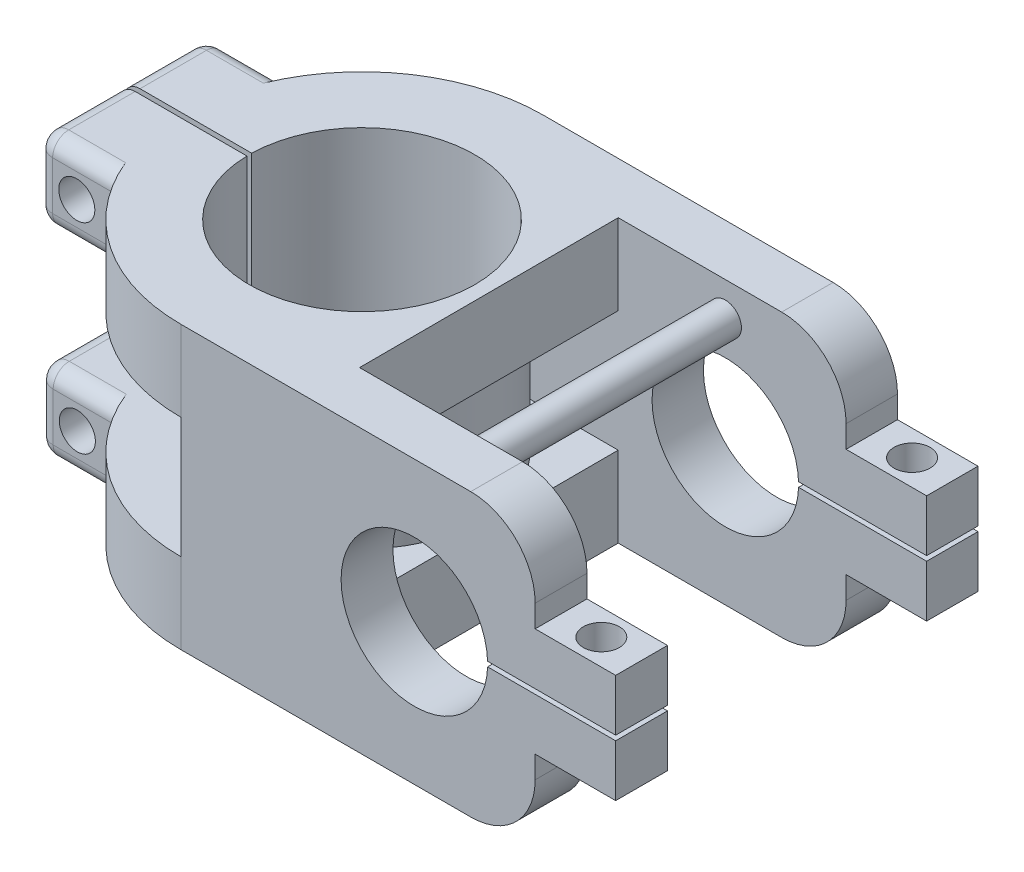
SolidWorks part; units mm, degrees
ref_plane "Front Plane" through (0, 0, 0) normal (0, 0, 1) x (1, 0, 0)
ref_plane "Top Plane" through (0, 0, 0) normal (0, 1, 0) x (1, 0, 0)
ref_plane "Right Plane" through (0, 0, 0) normal (1, 0, 0) x (0, 0, -1)
sketch "Sketch2" plane through (0, 0, 0) normal (0, 1, 0) x (1, 0, 0)
  circle A0 centre (0, 0) radius 17.78
  circle A2 centre (0, 0) radius 28.575
  dimension "D1" = 35.56
  dimension "D2" = 57.15
extrude "Boss-Extrude3" add sketch "Sketch2" along normal blind 12.7
sketch "Sketch3" plane through (0, 12.7, 0) normal (0, 1, 0) x (1, 0, 0)
  line L0 (0, 0) -> (20.2056, -20.2056) construction
  line L1 (0, 0) -> (20.2056, 20.2056) construction
  line L2 (0, 0) -> (-28.575, 0) construction
  line L3 (-25.3321, 0) -> (-25.3321, 13.2218) construction
  line L4 (-25.3321, 13.2218) -> (-25.3321, -13.2218)
  line L5 (-25.3321, 13.2218) -> (-36.1866, 13.2218)
  line L6 (-36.1866, 13.2218) -> (-36.1866, -13.2218)
  line L7 (-36.1866, -13.2218) -> (-25.3321, -13.2218)
  circle A0 centre (0, 0) radius 28.575 construction
extrude "Cut-Extrude1" cut sketch "Sketch3" against normal blind 12.7
sketch "Sketch4" plane through (0, 12.7, 0) normal (0, 1, 0) x (1, 0, 0)
  line L0 (0, 0) -> (-25.3321, 0) construction
  line L1 (-25.3321, -13.2218) -> (-25.3321, 13.2218) construction
  line L2 (-16.3768, 0) -> (-16.3768, 0.381)
  line L3 (-16.3768, 0) -> (-16.3768, -0.381)
  line L4 (-16.3768, 0.381) -> (-26.0036, 0.381)
  line L5 (-16.3768, -0.381) -> (-26.0036, -0.381)
  line L6 (-26.0036, -0.381) -> (-26.0036, 0.381)
  dimension "D1" = 0.762
extrude "Cut-Extrude2" cut sketch "Sketch4" against normal blind 12.7
sketch "Sketch5" plane through (-25.3321, 0, 0) normal (-1, 0, 0) x (0, 0, 1)
  line L1 (0.381, 12.7) -> (13.2218, 12.7)
  line L2 (0.381, 12.7) -> (0.381, 0)
  line L3 (0.381, 0) -> (13.2218, 0)
  line L4 (13.2218, 12.7) -> (13.2218, 0)
extrude "Boss-Extrude4" add sketch "Sketch5" along normal blind 12.7
sketch "Sketch6" plane through (-25.3321, 0, 0) normal (-1, 0, 0) x (0, 0, 1)
  line L1 (-13.2218, 12.7) -> (-0.381, 12.7)
  line L2 (-13.2218, 12.7) -> (-13.2218, 0)
  line L3 (-13.2218, 0) -> (-0.381, 0)
  line L4 (-0.381, 12.7) -> (-0.381, 0)
extrude "Boss-Extrude5" add sketch "Sketch6" along normal blind 12.7
sketch "Sketch7" plane through (0, 0, 13.2218) normal (0, 0, 1) x (1, 0, 0)
  line L0 (-31.6821, 12.7) -> (-31.6821, 0) construction
  line L1 (-38.0321, 12.7) -> (-25.3321, 12.7) construction
  line L2 (-38.0321, 0) -> (-25.3321, 0) construction
  circle A0 centre (-31.6821, 6.35) radius 2.8448
extrude "Cut-Extrude3" cut sketch "Sketch7" against normal blind 33.02
fillet "Fillet1" radius 2.54 1 edges at (-38.0321, 6.35, 13.2218)
fillet "Fillet2" radius 2.54 1 edges at (-38.0321, 6.35, -13.2218)
fillet "Fillet3" radius 2.54 3 edges at (-30.4121, 12.7, -13.2218) (-37.2882, 12.7, -12.4778) (-38.0321, 12.7, -5.5314)
fillet "Fillet4" radius 2.54 3 edges at (-30.4121, 12.7, 13.2218) (-37.2882, 12.7, 12.4778) (-38.0321, 12.7, 5.5314)
fillet "Fillet5" radius 2.54 3 edges at (-30.4121, 0, -13.2218) (-37.2882, 0, -12.4778) (-38.0321, 0, -5.5314)
fillet "Fillet6" radius 2.54 3 edges at (-30.4121, 0, 13.2218) (-37.2882, 0, 12.4778) (-38.0321, 0, 5.5314)
sketch "Sketch8" plane through (0, 12.7, 0) normal (0, 1, 0) x (1, 0, 0)
  circle A0 centre (0, 0) radius 18.7388
  circle A1 centre (0, 0) radius 17.78
extrude "Boss-Extrude6" add sketch "Sketch8" along normal blind 19.05
sketch "Sketch9" plane through (0, 31.75, 0) normal (0, 1, 0) x (1, 0, 0)
  circle A0 centre (0, 0) radius 28.575
extrude "Boss-Extrude7" add sketch "Sketch9" along normal blind 12.7
sketch "Sketch12" plane through (0, 44.45, 0) normal (0, 1, 0) x (1, 0, 0)
  line L0 (0, 0) -> (-28.575, 0) construction
  line L1 (-25.2365, 13.4034) -> (-25.2365, -13.4034)
  line L2 (-25.2365, 13.4034) -> (-36.6122, 13.4034)
  line L3 (-25.2365, -13.4034) -> (-36.6122, -13.4034)
  line L4 (-36.6122, -13.4034) -> (-36.6122, 13.4034)
  circle A0 centre (0, 0) radius 28.575 construction
extrude "Cut-Extrude4" cut sketch "Sketch12" against normal blind 12.7
sketch "Sketch13" plane through (-25.2365, 0, 0) normal (-1, 0, 0) x (0, 0, 1)
  line L0 (-18.7388, 31.75) -> (18.7388, 31.75) construction
  line L1 (-13.4034, 44.45) -> (13.4034, 44.45)
  line L2 (-13.4034, 44.45) -> (-13.4034, 31.75)
  line L3 (-13.4034, 31.75) -> (13.4034, 31.75)
  line L4 (13.4034, 44.45) -> (13.4034, 31.75)
  line L5 (13.4034, 31.75) -> (-13.4034, 31.75) construction
extrude "Boss-Extrude8" add sketch "Sketch13" along normal blind 12.7
sketch "Sketch14" plane through (0, 44.45, 0) normal (0, 1, 0) x (1, 0, 0)
  circle A0 centre (0, 0) radius 17.78
extrude "Cut-Extrude5" cut sketch "Sketch14" against normal blind 12.7
sketch "Sketch15" plane through (0, 44.45, 0) normal (0, 1, 0) x (1, 0, 0)
  line L0 (-37.9365, 0) -> (0, 0)
  line L1 (-37.9365, -13.4034) -> (-37.9365, 13.4034) construction
  line L2 (0, 0) -> (0, 0.381)
  line L3 (0, 0.381) -> (-38.0321, 0.381)
  line L4 (-38.0321, 0.381) -> (-37.9365, 0)
  line L5 (0, 0) -> (0, -0.381)
  line L6 (0, -0.381) -> (-37.9365, -0.381)
  line L7 (-37.9365, -0.381) -> (-37.9365, 0)
  line L8 (-37.9365, 0) -> (0, 0)
  circle M6 centre (0, 0) radius 17.78
  line M9 (-37.9365, 13.4034) -> (-37.9365, -13.4034)
  dimension "D1" = 0.381
extrude "Cut-Extrude6" cut sketch "Sketch15" against normal blind 12.7 contours L3 L0 M6 M9
sketch "Sketch16" plane through (0, 44.45, 0) normal (0, 1, 0) x (1, 0, 0)
  line L6 (-37.9365, 0) -> (-16.9968, 0)
  line L7 (-37.9365, 0) -> (-37.9365, -0.381)
  line L8 (-37.9365, -0.381) -> (-16.9968, -0.381)
  line L9 (-16.9968, 0) -> (-16.9968, -0.381)
  dimension "D1" = 0.381
extrude "Cut-Extrude7" cut sketch "Sketch16" against normal blind 12.7
fillet "Fillet7" radius 2.54 1 edges at (-37.9365, 44.45, -6.8922)
fillet "Fillet8" radius 2.54 1 edges at (-37.9365, 44.45, 6.8922)
fillet "Fillet9" radius 2.54 1 edges at (-37.9365, 31.75, -6.8922)
fillet "Fillet10" radius 2.54 1 edges at (-37.9365, 31.75, 6.8922)
fillet "Fillet11" radius 2.54 5 edges at (-30.3165, 31.75, 13.4034) (-37.1925, 32.4939, 13.4034) (-30.3165, 44.45, 13.4034) (-37.1925, 43.7061, 13.4034) (-37.9365, 38.1, 13.4034)
fillet "Fillet12" radius 2.54 5 edges at (-30.3165, 44.45, -13.4034) (-37.1925, 43.7061, -13.4034) (-30.3165, 31.75, -13.4034) (-37.1925, 32.4939, -13.4034) (-37.9365, 38.1, -13.4034)
sketch "Sketch17" plane through (0, 0, 13.4034) normal (0, 0, 1) x (1, 0, 0)
  line L0 (-25.2365, 38.1) -> (-37.9365, 38.1) construction
  line L1 (-25.2365, 34.29) -> (-25.2365, 41.91) construction
  line L2 (-37.9365, 34.29) -> (-37.9365, 41.91) construction
  circle A0 centre (-31.5865, 38.1) radius 2.8448
extrude "Cut-Extrude8" cut sketch "Sketch17" against normal blind 29.464
sketch "Sketch19" plane through (0, 31.75, 0) normal (0, 1, 0) x (1, 0, 0)
  line L5 (-18.7349, 0.381) -> (-16.9078, 0.381)
  line L6 (-18.7349, 0.381) -> (-18.7349, -0.381)
  line L7 (-18.7349, -0.381) -> (-16.9078, -0.381)
  line L8 (-16.9078, 0.381) -> (-16.9078, -0.381)
extrude "Cut-Extrude13" cut sketch "Sketch19" against normal blind 29.464
sketch "Sketch22" plane through (0, 12.7, 0) normal (0, 1, 0) x (1, 0, 0)
  line L0 (0, 0) -> (0, -18.7388) construction
  line L1 (0, -18.7388) -> (0, -20.3979) construction
  line L2 (0, -20.3979) -> (0, -28.575)
  line L3 (0, -28.575) -> (55.88, -28.575)
  line L4 (55.88, -28.575) -> (55.88, -20.3979)
  line L5 (55.88, -20.3979) -> (0, -20.3979)
  arc A0 (-18.7349, -0.381) -> (-18.7349, 0.381) centre (0, 0) ccw construction
  arc A1 (-26.5034, -10.6818) -> (-26.5034, 10.6818) centre (0, 0) ccw construction
  dimension "D1" = 55.88
extrude "Boss-Extrude12" add sketch "Sketch22" along normal blind 31.75 and the other way blind 12.7
sketch "Sketch23" plane through (0, 12.7, 0) normal (0, 1, 0) x (1, 0, 0)
  line L0 (0, -20.3979) -> (0, -18.6659) construction
  line L1 (0, 18.7388) -> (0, 20.4709) construction
  line L2 (0, 20.4709) -> (0, 28.575)
  line L3 (0, 28.575) -> (55.88, 28.575)
  line L4 (0, 20.4709) -> (55.88, 20.4709)
  line L5 (55.88, 20.4709) -> (55.88, 28.575)
  arc A0 (-18.7349, -0.381) -> (-18.7349, 0.381) centre (0, 0) ccw construction
  arc A1 (20.0114, -20.3979) -> (-26.5034, 10.6818) centre (0, 0) ccw construction
  dimension "D1" = 1.7321
  dimension "D2" = 55.88
extrude "Boss-Extrude13" add sketch "Sketch23" along normal blind 31.75 and the other way blind 12.7
sketch "Sketch24" plane through (0, 0, -28.575) normal (0, 0, -1) x (-1, 0, 0)
  line L0 (-17.78, 22.225) -> (-55.88, 22.225) construction
  line L2 (-17.78, 44.45) -> (-17.78, 0) construction
  line L3 (-55.88, 44.45) -> (0, 44.45) construction
  line L4 (-55.88, 0) -> (-55.88, 44.45) construction
  circle A0 centre (-36.83, 22.225) radius 11.557
extrude "Cut-Extrude14" cut sketch "Sketch24" against normal blind 67.31
fillet "Fillet13" radius 10.16 1 edges at (55.88, 44.45, 24.4865)
fillet "Fillet14" radius 10.16 1 edges at (55.88, 0, 24.4865)
fillet "Fillet15" radius 10.16 1 edges at (55.88, 44.45, -24.5229)
fillet "Fillet16" radius 10.16 1 edges at (55.88, 0, -24.5229)
sketch "Sketch25" plane through (0, 44.45, 0) normal (0, 1, 0) x (1, 0, 0)
  line L0 (28.575, 0.0522) -> (28.575, 20.4709)
  line L1 (19.9368, 20.4709) -> (45.72, 20.4709) construction
  line L2 (28.575, 20.4709) -> (19.9368, 20.4709)
  line L3 (19.9368, 20.4709) -> (20.0114, -20.3979)
  line L4 (20.0114, -20.3979) -> (28.575, -20.3979)
  line L5 (45.72, -20.3979) -> (20.0114, -20.3979) construction
  line L6 (28.575, -20.3979) -> (28.575, 0.0522)
  arc A0 (20.0114, -20.3979) -> (19.9368, 20.4709) centre (0, 0) ccw construction
extrude "Cut-Extrude15" cut sketch "Sketch25" against normal blind 67.31
sketch "Sketch26" plane through (0, 0, -20.4709) normal (0, 0, 1) x (1, 0, 0)
  line L0 (36.83, 33.782) -> (36.83, 44.45) construction
  line L1 (19.9368, 44.45) -> (45.72, 44.45) construction
  circle A0 centre (36.83, 22.225) radius 11.557 construction
  circle A1 centre (36.83, 39.116) radius 2.54
extrude "Boss-Extrude14" add sketch "Sketch26" along normal blind 43.434
sketch "Sketch27" plane through (0, 0, 28.575) normal (0, 0, 1) x (1, 0, 0)
  line L0 (48.387, 22.225) -> (55.88, 22.225) construction
  line L1 (55.88, 10.16) -> (55.88, 34.29) construction
  line L2 (57.8595, 22.225) -> (46.9704, 22.225)
  line L3 (46.9704, 22.225) -> (46.9704, 22.606)
  line L4 (46.9704, 22.606) -> (57.8595, 22.606)
  line L5 (57.8595, 22.606) -> (57.8595, 22.225)
  circle A0 centre (36.83, 22.225) radius 11.557 construction
  dimension "D1" = 0.381
extrude "Cut-Extrude16" cut sketch "Sketch27" against normal blind 64.516
sketch "Sketch28" plane through (0, 0, 28.575) normal (0, 0, 1) x (1, 0, 0)
  line L0 (47.571, 22.225) -> (56.4711, 22.225)
  line L1 (56.4711, 22.225) -> (56.4711, 21.844)
  line L2 (56.4711, 21.844) -> (47.571, 21.844)
  line L3 (47.571, 21.844) -> (47.571, 22.225)
  dimension "D1" = 0.381
extrude "Cut-Extrude17" cut sketch "Sketch28" against normal blind 64.516
sketch "Sketch29" plane through (55.88, 0, 0) normal (1, 0, 0) x (0, 0, -1)
  line L0 (-28.575, 22.606) -> (-20.3979, 22.606)
  line L1 (-20.3979, 22.606) -> (-20.3979, 30.7831)
  line L2 (-20.3979, 22.606) -> (-20.3979, 34.29) construction
  line L3 (-20.3979, 30.7831) -> (-28.575, 30.7831)
  line L4 (-28.575, 22.606) -> (-28.575, 34.29) construction
  line L5 (-28.575, 30.7831) -> (-28.575, 22.606)
  dimension "D1" = 8.1771
extrude "Boss-Extrude15" add sketch "Sketch29" along normal blind 12.7
sketch "Sketch30" plane through (55.88, 0, 0) normal (1, 0, 0) x (0, 0, -1)
  line L0 (-28.575, 21.844) -> (-20.3979, 21.844)
  line L1 (-20.3979, 21.844) -> (-20.3979, 13.6669)
  line L2 (-20.3979, 10.16) -> (-20.3979, 21.844) construction
  line L3 (-20.3979, 13.6669) -> (-28.575, 13.6669)
  line L4 (-28.575, 10.16) -> (-28.575, 21.844) construction
  line L5 (-28.575, 13.6669) -> (-28.575, 21.844)
extrude "Boss-Extrude16" add sketch "Sketch30" along normal blind 12.7
sketch "Sketch31" plane through (0, 30.7831, 0) normal (0, 1, 0) x (1, 0, 0)
  line L0 (62.23, -20.3979) -> (62.23, -28.575) construction
  line L1 (68.58, -20.3979) -> (55.88, -20.3979) construction
  line L2 (68.58, -28.575) -> (55.88, -28.575) construction
  circle A0 centre (62.23, -24.4865) radius 2.8448
extrude "Cut-Extrude18" cut sketch "Sketch31" against normal blind 22.098
sketch "Sketch34" plane through (55.88, 0, 0) normal (1, 0, 0) x (0, 0, -1)
  line L0 (28.575, 22.606) -> (28.575, 30.7831)
  line L1 (28.575, 22.606) -> (28.575, 34.29) construction
  line L2 (28.575, 30.7831) -> (20.4709, 30.7831)
  line L3 (20.4709, 22.606) -> (20.4709, 34.29) construction
  line L4 (20.4709, 30.7831) -> (20.4709, 22.606)
  line L5 (20.4709, 22.606) -> (28.575, 22.606)
extrude "Boss-Extrude17" add sketch "Sketch34" along normal blind 12.7
sketch "Sketch35" plane through (55.88, 0, 0) normal (1, 0, 0) x (0, 0, -1)
  line L0 (28.575, 21.844) -> (28.575, 13.6669)
  line L1 (28.575, 10.16) -> (28.575, 21.844) construction
  line L2 (28.575, 13.6669) -> (20.4709, 13.6669)
  line L3 (20.4709, 10.16) -> (20.4709, 21.844) construction
  line L4 (20.4709, 13.6669) -> (20.4709, 21.844)
  line L5 (20.4709, 21.844) -> (28.575, 21.844)
extrude "Boss-Extrude18" add sketch "Sketch35" along normal blind 12.7
sketch "Sketch36" plane through (0, 30.7831, 0) normal (0, 1, 0) x (1, 0, 0)
  line L0 (62.23, 28.575) -> (62.23, 20.4709) construction
  line L1 (68.58, 28.575) -> (55.88, 28.575) construction
  line L2 (68.58, 20.4709) -> (55.88, 20.4709) construction
  circle A0 centre (62.23, 24.5229) radius 2.8448
extrude "Cut-Extrude19" cut sketch "Sketch36" against normal blind 27.686
